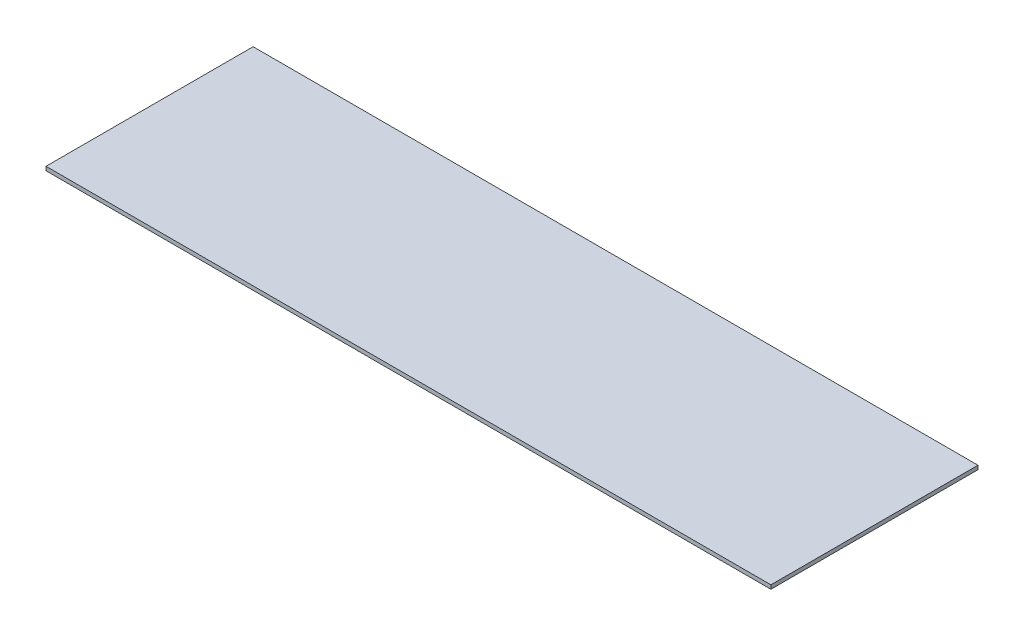
SolidWorks part; units mm, degrees
ref_plane "Front Plane" through (0, 0, 0) normal (0, 0, 1) x (1, 0, 0)
ref_plane "Top Plane" through (0, 0, 0) normal (0, 1, 0) x (1, 0, 0)
ref_plane "Right Plane" through (0, 0, 0) normal (1, 0, 0) x (0, 0, -1)
sketch "Sketch1" plane through (0, 0, 0) normal (0, 1, 0) x (1, 0, 0)
  line L1 (-14, -4) -> (14, -4)
  line L2 (-14, -4) -> (-14, 4)
  line L3 (-14, 4) -> (14, 4)
  line L4 (14, -4) -> (14, 4)
  line L5 (-14, -4) -> (14, 4) construction
  line L6 (-14, 4) -> (14, -4) construction
  point P0 (0, 0)
  dimension "D1" = 8
  dimension "D2" = 28
extrude "Boss-Extrude1" add sketch "Sketch1" along normal blind 0.15
